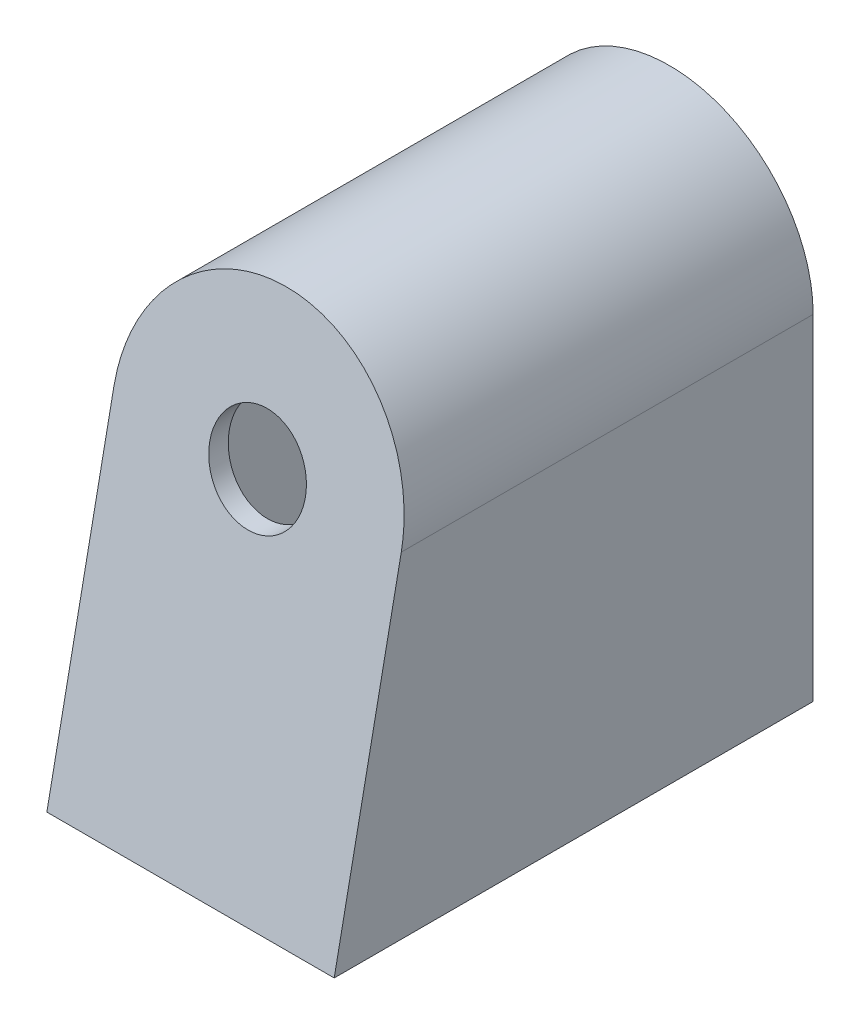
SolidWorks part; units mm, degrees
ref_plane "Plan de face" through (0, 0, 0) normal (0, 0, 1) x (1, 0, 0)
ref_plane "Plan de dessus" through (0, 0, 0) normal (0, 1, 0) x (1, 0, 0)
ref_plane "Plan de droite" through (0, 0, 0) normal (1, 0, 0) x (0, 0, -1)
sketch "Esquisse1" plane through (0, 0, 0) normal (0, 0, 1) x (1, 0, 0)
  line L1 (-15, -17.5) -> (15, -17.5)
  line L2 (-15, -17.5) -> (-15, 17.5)
  line L4 (15, -17.5) -> (15, 17.5)
  line L5 (-15, -17.5) -> (15, 17.5) construction
  line L6 (-15, 17.5) -> (15, -17.5) construction
  arc A0 (15, 17.5) -> (-15, 17.5) centre (0, 17.5) ccw
  circle A1 centre (0, 17.5) radius 5
  point P0 (0, 0)
  dimension "D2" = 10
  dimension "D3" = 50
  dimension "D1" = 30
extrude "Boss.-Extru.1" add sketch "Esquisse1" against normal blind 50
sketch "Esquisse2" plane through (0, 0, 0) normal (1, 0, 0) x (0, 0, -1)
  line L0 (0, -17.5) -> (10, 32.5)
  line L1 (50, 32.5) -> (0, 32.5) construction
  line L2 (10, 32.5) -> (0, 32.5)
  line L3 (0, 32.5) -> (0, 17.5) construction
  line L4 (0, 32.5) -> (0, -17.5)
  dimension "D1" = 10
extrude "Enlèv. mat.-Extru.1" cut sketch "Esquisse2" against normal through all both and the other way through all
sketch "Esquisse3" plane through (0, 0, -50) normal (0, 0, -1) x (-1, 0, 0)
  line L12 (-13, 17.5) -> (-13, -15.5)
  line L13 (-13, -15.5) -> (13, -15.5)
  line L14 (13, -15.5) -> (13, 17.5)
  line L15 (-13, 17.5) -> (-13, -15.5)
  line L16 (-13, -15.5) -> (13, -15.5)
  line L17 (13, -15.5) -> (13, 17.5)
  arc A4 (13, 17.5) -> (-13, 17.5) centre (0, 17.5) ccw
  arc A5 (13, 17.5) -> (-13, 17.5) centre (0, 17.5) ccw
  dimension "D1" = 2
extrude "Enlèv. mat.-Extru.2" cut sketch "Esquisse3" against normal offset from surface (47.5604 mm away) 2
